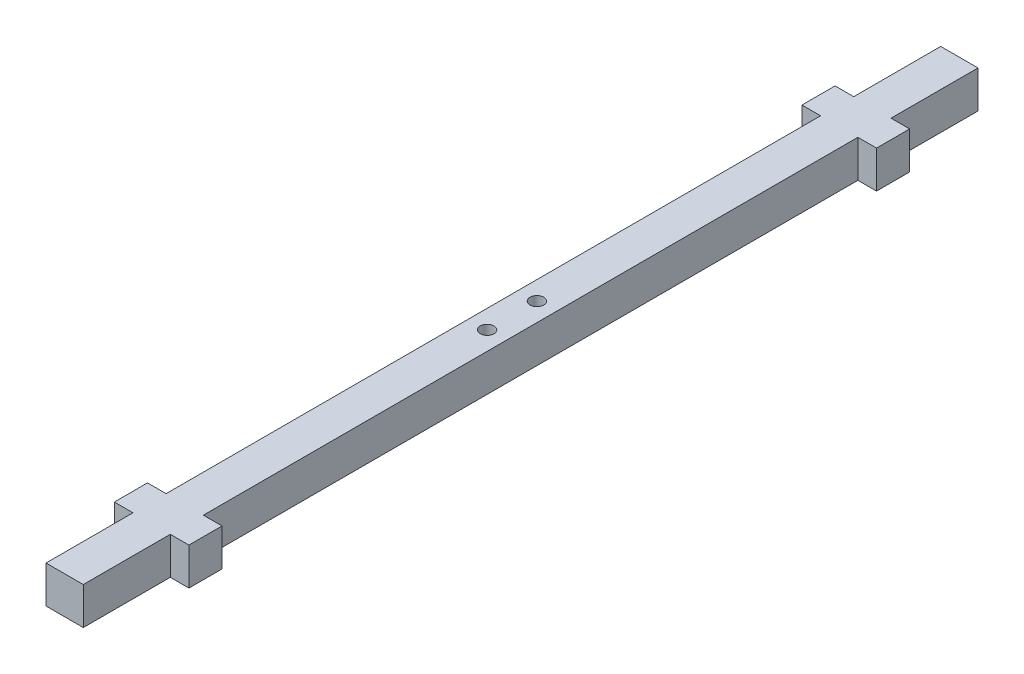
SolidWorks part; units mm, degrees
ref_plane "Front Plane" through (0, 0, 0) normal (0, 0, 1) x (1, 0, 0)
ref_plane "Top Plane" through (0, 0, 0) normal (0, 1, 0) x (1, 0, 0)
ref_plane "Right Plane" through (0, 0, 0) normal (1, 0, 0) x (0, 0, -1)
sketch "Sketch1" plane through (0, 0, 0) normal (0, 0, 1) x (1, 0, 0)
  line L1 (-4.5, -4.5) -> (4.5, -4.5)
  line L2 (-4.5, -4.5) -> (-4.5, 4.5)
  line L3 (-4.5, 4.5) -> (4.5, 4.5)
  line L4 (4.5, -4.5) -> (4.5, 4.5)
  line L5 (-4.5, -4.5) -> (4.5, 4.5) construction
  line L6 (-4.5, 4.5) -> (4.5, -4.5) construction
  point P0 (0, 0)
  dimension "D1" = 9
extrude "Boss-Extrude1" add sketch "Sketch1" along normal mid plane 216
sketch "Sketch2" plane through (0, 0, 0) normal (0, 1, 0) x (1, 0, 0)
  line L5 (0, -83) -> (0, 83) construction
  line L6 (-9, 79) -> (9, 79)
  line L11 (-9, 79) -> (-9, 87)
  line L12 (-9, 87) -> (9, 87)
  line L14 (9, 79) -> (9, 87)
  line L15 (-9, 79) -> (9, 87) construction
  line L16 (-9, 87) -> (9, 79) construction
  line L17 (-9, -87) -> (9, -87)
  line L18 (-9, -87) -> (-9, -79)
  line L19 (-9, -79) -> (9, -79)
  line L20 (9, -87) -> (9, -79)
  line L21 (-9, -87) -> (9, -79) construction
  line L22 (-9, -79) -> (9, -87) construction
  line L23 (4.5, 108) -> (-4.5, 108) construction
  point P0 (0, 83)
  point P5 (0, -83)
  point P12 (0, 0)
  dimension "D1" = 21
  dimension "D2" = 18
  dimension "D3" = 8
extrude "Boss-Extrude2" add sketch "Sketch2" along normal mid plane 9
sketch "Sketch3" plane through (0, 4.5, 0) normal (0, 1, 0) x (1, 0, 0)
  line L0 (0, -6) -> (0, 6) construction
  circle A0 centre (0, 6) radius 1.65
  circle A1 centre (0, -6) radius 1.65
  point P4 (0, 0)
  dimension "D1" = 3.3
  dimension "D2" = 12
extrude "Cut-Extrude1" cut sketch "Sketch3" against normal through all both and the other way through all
